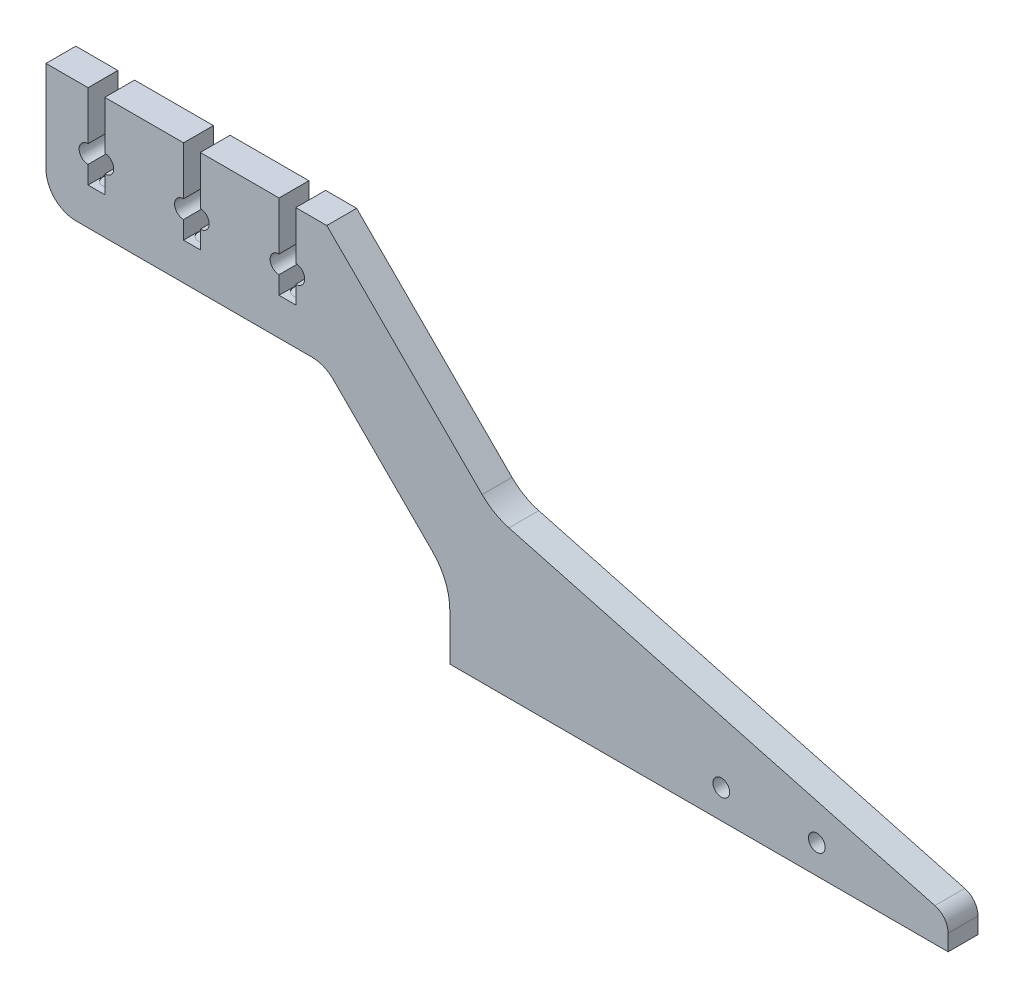
SolidWorks part; units mm, degrees
ref_plane "前视基准面" through (0, 0, 0) normal (0, 0, 1) x (1, 0, 0)
ref_plane "上视基准面" through (0, 0, 0) normal (0, 1, 0) x (1, 0, 0)
ref_plane "右视基准面" through (0, 0, 0) normal (1, 0, 0) x (0, 0, -1)
sketch "草图1" plane through (0, 0, 0) normal (0, 0, 1) x (1, 0, 0)
  line L0 (-57.805, 53.3326) -> (-44.605, 53.3326)
  line L1 (-41.805, 53.3326) -> (-28.605, 53.3326)
  line L2 (-25.805, 53.3326) -> (-20.605, 53.3326)
  line L3 (-67.6482, 53.3326) -> (-60.605, 53.3326)
  line L4 (-20.605, 53.3326) -> (5.4208, 27.3067)
  line L5 (9.9037, 24.7186) -> (81.2708, 5.5958)
  line L6 (83.4943, 2.698) -> (83.4943, 0)
  line L7 (83.4943, 0) -> (0, 0)
  line L8 (0, 0) -> (0, 7.8579)
  line L9 (-2.9289, 14.9289) -> (-19.5247, 31.5247)
  line L10 (-23.0603, 32.9892) -> (-62.6482, 32.9892)
  line L11 (-60.605, 53.3326) -> (-60.605, 45.207)
  line L12 (-57.805, 45.207) -> (-57.805, 53.3326)
  line L13 (-60.605, 42.207) -> (-60.605, 39.207)
  line L14 (-60.605, 39.207) -> (-57.805, 39.207)
  line L15 (-57.805, 39.207) -> (-57.805, 42.207)
  line L16 (-44.605, 53.3326) -> (-44.605, 45.207)
  line L17 (-41.805, 45.207) -> (-41.805, 53.3326)
  line L18 (-44.605, 42.207) -> (-44.605, 39.207)
  line L19 (-44.605, 39.207) -> (-41.805, 39.207)
  line L20 (-41.805, 39.207) -> (-41.805, 42.207)
  line L21 (-28.605, 53.3326) -> (-28.605, 45.207)
  line L22 (-25.805, 45.207) -> (-25.805, 53.3326)
  line L23 (-28.605, 42.207) -> (-28.605, 39.207)
  line L24 (-28.605, 39.207) -> (-25.805, 39.207)
  line L25 (-25.805, 39.207) -> (-25.805, 42.207)
  line L26 (-67.6482, 37.9892) -> (-67.6482, 53.3326)
  arc A4 (5.4208, 27.3067) -> (9.9037, 24.7186) centre (12.4919, 34.3778) ccw
  arc A5 (83.4943, 2.698) -> (81.2708, 5.5958) centre (80.4943, 2.698) ccw
  arc A6 (0, 7.8579) -> (-2.9289, 14.9289) centre (-10, 7.8579) ccw
  arc A7 (-19.5247, 31.5247) -> (-23.0603, 32.9892) centre (-23.0603, 27.9892) ccw
  arc A8 (-67.6482, 37.9892) -> (-62.6482, 32.9892) centre (-62.6482, 37.9892) ccw
  arc A9 (-60.605, 45.207) -> (-60.605, 42.207) centre (-60.605, 43.707) ccw
  arc A10 (-57.805, 42.207) -> (-57.805, 45.207) centre (-57.805, 43.707) ccw
  arc A11 (-44.605, 45.207) -> (-44.605, 42.207) centre (-44.605, 43.707) ccw
  arc A12 (-41.805, 42.207) -> (-41.805, 45.207) centre (-41.805, 43.707) ccw
  arc A13 (-28.605, 45.207) -> (-28.605, 42.207) centre (-28.605, 43.707) ccw
  arc A14 (-25.805, 42.207) -> (-25.805, 45.207) centre (-25.805, 43.707) ccw
  circle A15 centre (45.4903, 4.8384) radius 1.4
  circle A16 centre (61.4903, 4.8384) radius 1.4
extrude "凸台-拉伸1" add sketch "草图1" along normal mid plane 5
sketch "草图2" plane through (0, 39.207, 0) normal (0, 1, 0) x (1, 0, 0)
  circle A0 centre (-59.205, 0) radius 1.4
  circle A1 centre (-43.205, 0) radius 1.4
  circle A2 centre (-27.205, 0) radius 1.4
extrude "切除-拉伸1" cut sketch "草图2" against normal blind 0.1
